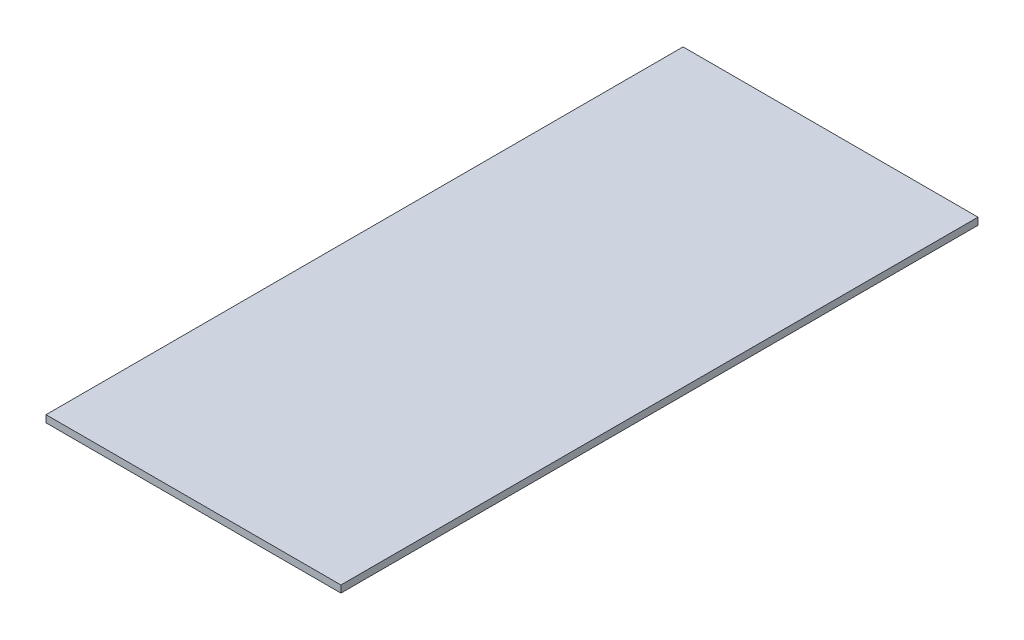
SolidWorks part; units mm, degrees
ref_plane "Plan de face" through (0, 0, 0) normal (0, 0, 1) x (1, 0, 0)
ref_plane "Plan de dessus" through (0, 0, 0) normal (0, 1, 0) x (1, 0, 0)
ref_plane "Plan de droite" through (0, 0, 0) normal (1, 0, 0) x (0, 0, -1)
sketch "Esquisse1" plane through (0, 0, 0) normal (0, 1, 0) x (1, 0, 0)
  line L1 (0, 0) -> (125, 0)
  line L2 (0, 0) -> (0, 270)
  line L3 (0, 270) -> (125, 270)
  line L4 (125, 0) -> (125, 270)
  dimension "D1" = 270
  dimension "D2" = 125
extrude "Boss.-Extru.1" add sketch "Esquisse1" along normal blind 3
